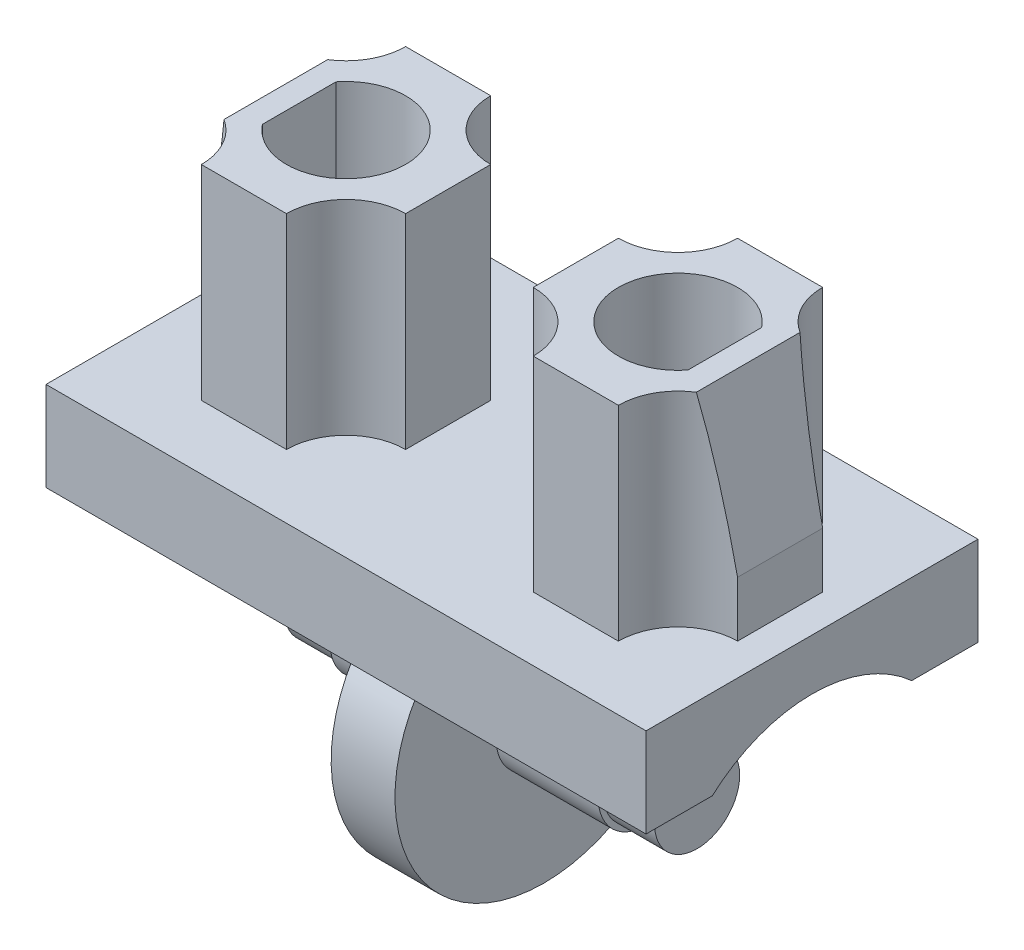
SolidWorks part; units mm, degrees
ref_plane "Front Plane" through (0, 0, 0) normal (0, 0, 1) x (1, 0, 0)
ref_plane "Top Plane" through (0, 0, 0) normal (0, 1, 0) x (1, 0, 0)
ref_plane "Right Plane" through (0, 0, 0) normal (1, 0, 0) x (0, 0, -1)
sketch "Sketch2" plane through (0, 0, 0) normal (1, 0, 0) x (0, 0, -1)
  line L0 (2.3431, 2.6) -> (3.9, 2.6)
  line L1 (-3.9, 4.7) -> (3.9, 4.7)
  line L2 (-3.9, 4.7) -> (-3.9, 2.6)
  line L3 (-3.9, 2.6) -> (-2.3431, 2.6)
  line L4 (3.9, 4.7) -> (3.9, 2.6)
  circle A0 centre (0, 0) radius 3.5
  dimension "D1" = 7
  dimension "D5" = 4.7
  dimension "D2" = 7.8
  dimension "D3" = 2.1
  dimension "D4" = 3.9
extrude "Boss-Extrude1" add sketch "Sketch2" along normal mid plane 14.1 contours A0 L0 L4 L1 L2 L3
sketch "Sketch4" plane through (0, 0, 0) normal (1, 0, 0) x (0, 0, -1)
  circle A0 centre (0, 0) radius 3.5
  dimension "D1" = 7
extrude "Boss-Extrude2" add sketch "Sketch4" along normal mid plane 1.5
sketch "Sketch5" plane through (0.75, 0, 0) normal (1, 0, 0) x (0, 0, -1)
  circle A0 centre (0, 0) radius 1.125
  dimension "D1" = 2.25
extrude "Boss-Extrude3" add sketch "Sketch5" along normal blind 2.4
sketch "Sketch6" plane through (3.15, 0, 0) normal (1, 0, 0) x (0, 0, -1)
  circle A0 centre (0, 0) radius 1
  dimension "D1" = 2
extrude "Boss-Extrude4" add sketch "Sketch6" along normal blind 1.2
sketch "Sketch7" plane through (-0.75, 0, 0) normal (-1, 0, 0) x (0, 0, 1)
  circle A0 centre (0, 0) radius 1.125
  dimension "D1" = 2.25
extrude "Boss-Extrude5" add sketch "Sketch7" along normal blind 2.4
sketch "Sketch8" plane through (-3.15, 0, 0) normal (-1, 0, 0) x (0, 0, 1)
  circle A0 centre (0, 0) radius 1
  dimension "D1" = 2
extrude "Boss-Extrude6" add sketch "Sketch8" along normal blind 1.2
sketch "Sketch9" plane through (0, 4.7, 0) normal (0, 1, 0) x (1, 0, 0)
  line L0 (0, 9.4864) -> (0, -12.0277) construction
  line L1 (7.05, 3.9) -> (-7.05, 3.9) construction
  line L2 (2.9, -2.4) -> (4.9, -2.4)
  line L3 (1.5, -1) -> (1.5, 1)
  line L4 (2.9, 2.4) -> (4.9, 2.4)
  line L5 (6.3, -1) -> (6.3, 1)
  line L6 (-6.3, -1) -> (-6.3, 1)
  line L7 (-2.9, -2.4) -> (-4.9, -2.4)
  line L8 (-1.5, -1) -> (-1.5, 1)
  line L9 (-2.9, 2.4) -> (-4.9, 2.4)
  arc A1 (1.5, 1) -> (2.9, 2.4) centre (1.5, 2.4) ccw
  arc A2 (4.9, 2.4) -> (6.3, 1) centre (6.3, 2.4) ccw
  arc A3 (6.3, -1) -> (4.9, -2.4) centre (6.3, -2.4) ccw
  arc A4 (2.9, -2.4) -> (1.5, -1) centre (1.5, -2.4) ccw
  arc A5 (-4.9, 2.4) -> (-6.3, 1) centre (-6.3, 2.4) cw
  arc A6 (-6.3, -1) -> (-4.9, -2.4) centre (-6.3, -2.4) cw
  arc A7 (-2.9, -2.4) -> (-1.5, -1) centre (-1.5, -2.4) cw
  arc A8 (-1.5, 1) -> (-2.9, 2.4) centre (-1.5, 2.4) cw
  dimension "D5" = 1.4
  dimension "D6" = 1.4
  dimension "D1" = 1.5
  dimension "D2" = 4.8
  dimension "D3" = 4.8
  dimension "D4" = 1.5
extrude "Boss-Extrude8" add sketch "Sketch9" along normal blind 4.8
sketch "Sketch10" plane through (0, 9.5, 0) normal (0, 1, 0) x (1, 0, 0)
  line L0 (2.9, -2.4) -> (4.9, -2.4) construction
  line L1 (1.5, 1) -> (1.5, -1) construction
  line L2 (5, 0.866) -> (5, -0.866)
  line L3 (6.3, -1) -> (6.3, 1) construction
  line L4 (0, 6.3872) -> (0, -6.8685) construction
  line L5 (-5, 0.866) -> (-5, -0.866)
  arc A0 (5, 0.866) -> (5, -0.866) centre (3.9, 0) ccw
  arc A1 (-5, 0.866) -> (-5, -0.866) centre (-3.9, 0) cw
  dimension "D1" = 2.8
  dimension "D2" = 2.4
  dimension "D3" = 2.4
  dimension "D4" = 1.3
extrude "Cut-Extrude1" cut sketch "Sketch10" against normal blind 4.8
sketch "Sketch12" plane through (0, 0, 0) normal (0, 0, 1) x (1, 0, 0)
  line L0 (5.55, 9.5) -> (6.3, 9.5)
  line L1 (6.3, 9.5) -> (4.9, 9.5) construction
  line L2 (6.3, 9.5) -> (6.3, 6)
  line L3 (6.3, 9.5) -> (6.3, 4.7) construction
  line L4 (6.3, 6) -> (5.55, 9.5)
  line L5 (0, 14.4772) -> (0, -12.7379) construction
  line L6 (-6.3, 6) -> (-5.55, 9.5)
  line L7 (-5.55, 9.5) -> (-6.3, 9.5)
  line L8 (-6.3, 9.5) -> (-6.3, 6)
  dimension "D1" = 0.75
  dimension "D2" = 3.5
extrude "Cut-Extrude2" cut sketch "Sketch12" against normal through all both and the other way through all
